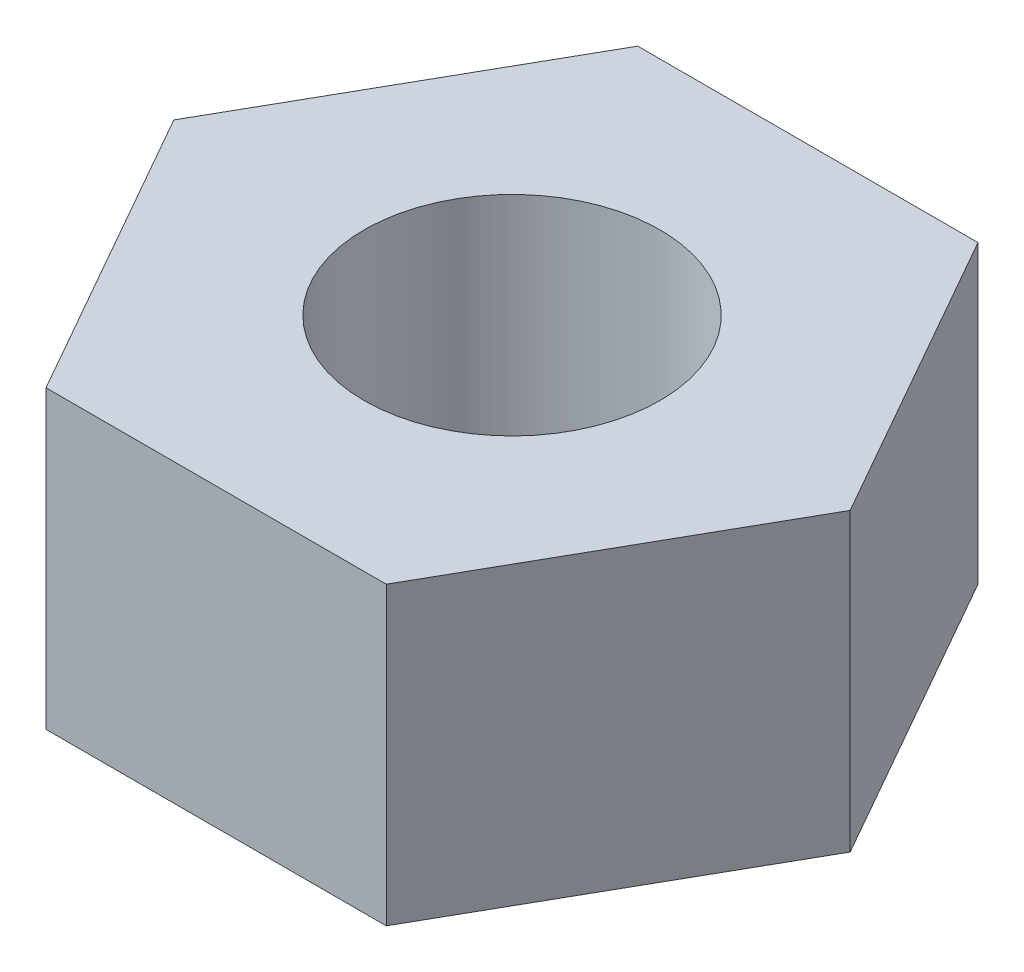
SolidWorks part; units mm, degrees
ref_plane "Front Plane" through (0, 0, 0) normal (0, 0, 1) x (1, 0, 0)
ref_plane "Top Plane" through (0, 0, 0) normal (0, 1, 0) x (1, 0, 0)
ref_plane "Right Plane" through (0, 0, 0) normal (1, 0, 0) x (0, 0, -1)
sketch "Sketch1" plane through (0, 0, 0) normal (0, 1, 0) x (1, 0, 0)
  line L0 (-5.7511, 10) -> (5.7489, 10)
  line L1 (5.7489, 10) -> (11.4278, 0)
  line L2 (11.4278, 0) -> (5.7489, -10)
  line L3 (5.7489, -10) -> (-5.7511, -10)
  line L4 (-5.7511, -10) -> (-11.43, 0)
  line L5 (-11.43, 0) -> (-5.7511, 10)
  circle A0 centre (0, 0) radius 5
  point P5 (0, 0)
  point P10 (0, 0)
  point P11 (0, 0)
  point P12 (0, 0)
  point P13 (10.9167, 0)
  point P14 (11.0361, 0)
  dimension "D1" = 10
  dimension "D2" = 11.5
  dimension "D3" = 20
  dimension "D4" = 11.43
extrude "Boss-Extrude1" add sketch "Sketch1" along normal blind 10
